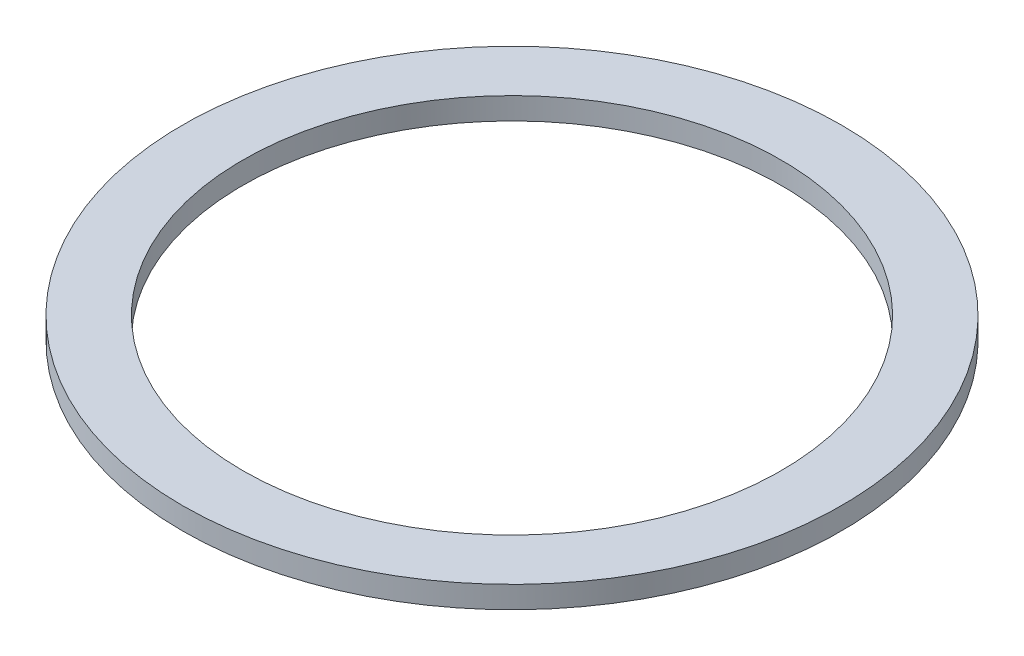
SolidWorks part; units mm, degrees
ref_plane "Front Plane" through (0, 0, 0) normal (0, 0, 1) x (1, 0, 0)
ref_plane "Top Plane" through (0, 0, 0) normal (0, 1, 0) x (1, 0, 0)
ref_plane "Right Plane" through (0, 0, 0) normal (1, 0, 0) x (0, 0, -1)
sketch "Sketch1" plane through (0, 0, 0) normal (0, 1, 0) x (-1, 0, 0)
  circle A0 centre (0, 0) radius 15
  circle A1 centre (0, 0) radius 12.25
  dimension "D1" = 30
  dimension "D2" = 24.5
extrude "Boss-Extrude1" add sketch "Sketch1" along normal blind 1
